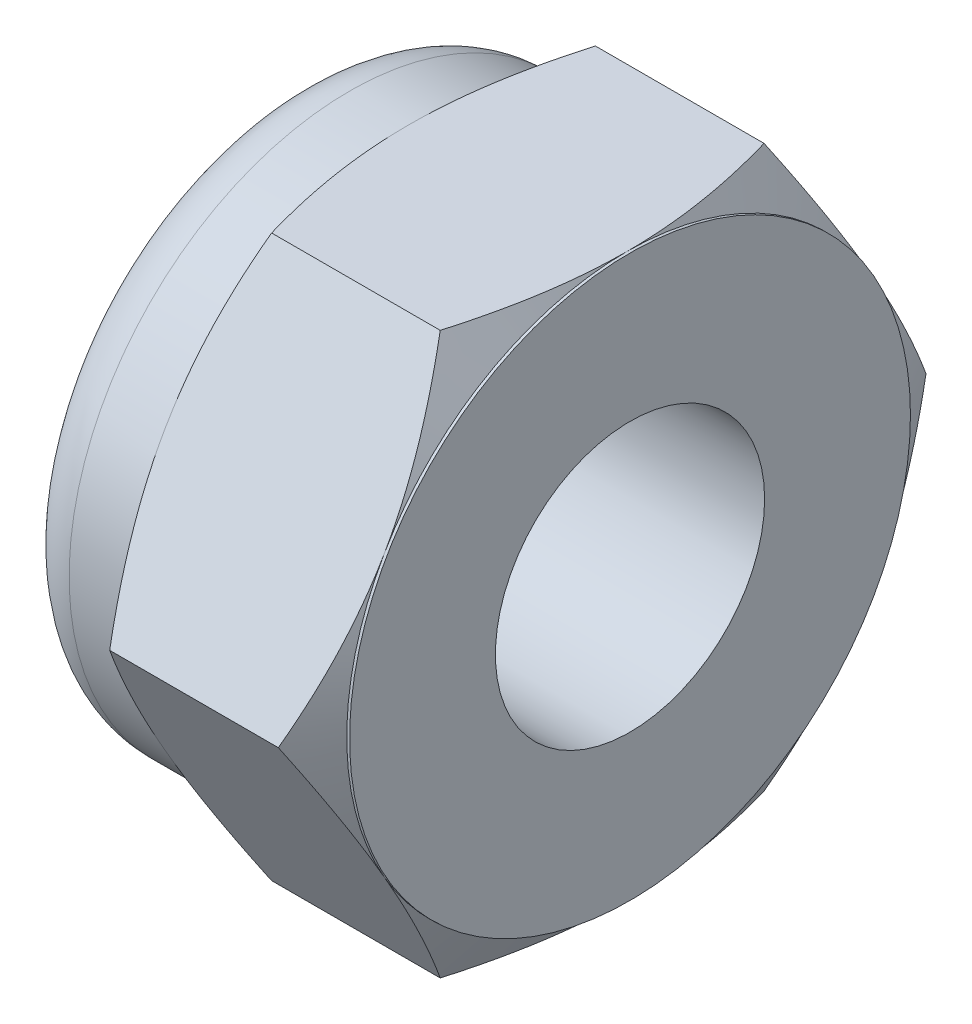
SolidWorks part; units mm, degrees
material " "
ref_plane "Ebene vorne" through (0, 0, 0) normal (0, 0, 1) x (1, 0, 0)
ref_plane "Ebene oben" through (0, 0, 0) normal (0, 1, 0) x (1, 0, 0)
ref_plane "Ebene rechts" through (0, 0, 0) normal (1, 0, 0) x (0, 0, -1)
sketch "Skizze6" plane through (0, 0, 0) normal (1, 0, 0) x (0, 0, -1)
  circle A0 centre (0, 0) radius 5
extrude "Grundkörper" add sketch "Skizze6" against normal blind 4 separate body
sketch "Skizze17" plane through (0, 0, 0) normal (0, 0, 1) x (1, 0, 0)
  line L0 (0, 0) -> (-4, 0) construction
  line L1 (3.3, 0) -> (-3.3, 0) construction
  line L2 (-4, 5) -> (-4, -5) construction
  line L3 (-0.05, 5) -> (-2, 8.3775)
  line L5 (-2, 8.3775) -> (-3.95, 5)
  line L6 (-3.95, 5) -> (-0.05, 5)
  line L7 (0, -5) -> (0, 5) construction
  line L8 (-2, 8.3775) -> (-2, 0) construction
  line L9 (0, 5) -> (-4, 5) construction
  dimension "D1" = 30
  dimension "D2" = 0.05
revolve "Rotation2" add sketch "Skizze17" angle 360 about L0
sketch "Skizze14" plane through (0, 0, 0) normal (1, 0, 0) x (0, 0, -1)
  line L1 (2.8868, -5) -> (5.7735, 0)
  line L2 (5.7735, 0) -> (2.8868, 5)
  line L3 (2.8868, 5) -> (-2.8868, 5)
  line L4 (-2.8868, 5) -> (-5.7735, 0)
  line L5 (-5.7735, 0) -> (-2.8868, -5)
  line L6 (-2.8868, -5) -> (2.8868, -5)
  circle A0 centre (0, 0) radius 5 construction
  circle A3 centre (0, 0) radius 8.3775 construction
  circle A4 centre (0, 0) radius 8.3775
extrude "Schnitt Sechskant" cut sketch "Skizze14" against normal through all
sketch "Skizze13" plane through (0, 0, 0) normal (1, 0, 0) x (0, 0, -1)
  circle A0 centre (0, 0) radius 2.4
extrude "Gewinde" cut sketch "Skizze13" against normal through all
cosmetic thread "Gewindedarstellung1"
sketch "Skizze18" plane through (0, 0, 0) normal (0, 0, 1) x (1, 0, 0)
  line L0 (0, 0) -> (-4, 0) construction
  line L1 (-4, 5) -> (-4, -5) construction
  line L2 (-4, 5) -> (-5, 5)
  line L3 (-6, 3) -> (-5, 3)
  line L4 (-6, 3) -> (-6, 4)
  line L5 (-4, 5) -> (-4, 4)
  line L8 (-4, 4) -> (-5, 4)
  line L9 (-5, 4) -> (-5, 3)
  arc A0 (-5, 5) -> (-6, 4) centre (-5, 4) ccw
  dimension "D1" = 1
  dimension "Sicherungsmutter_Höhe" = 6
revolve "Sicherungsmutter Rotation3" add sketch "Skizze18" angle 360 about L0
sketch "Skizze19" plane through (0, 0, 0) normal (0, 0, 1) x (1, 0, 0)
  line L0 (0, 0) -> (-3.0627, 0) construction
  line L1 (-5, 2.4) -> (-4, 2.4)
  line L2 (-5, 2.4) -> (-5, 4)
  line L3 (-5, 4) -> (-4, 4)
  line L4 (-4, 2.4) -> (-4, 4)
  line L6 (-5, -4) -> (-5, 4) construction
revolve "Sicherungsmutter Rotation4" add sketch "Skizze19" angle 360 about L0
sketch "Skizze20" [suppressed] plane through (0, 0, 0) normal (0, 0, 1) x (1, 0, 0)
  line L0 (0, 0) -> (-13, 0) construction
  line L1 (-13, 12) -> (-13, -12) construction
  line L2 (-13, 2.4) -> (-19, 2.4)
  line L3 (-19, 2.4) -> (-19, 12)
  line L4 (-19, 12) -> (-13, 12)
  line L5 (-13, 12) -> (-13, 2.4)
  line L6 (0, 2.4) -> (-13, 2.4) construction
  dimension "Kronenmutter_Höhe" = 8
revolve "Kronenmutter Rotation3" [suppressed] add sketch "Skizze20" angle 360 about L0
sketch "Skizze22" [suppressed] plane through (0, 0, 0) normal (0, 1, 0) x (1, 0, 0)
  line L0 (-19, 0) -> (-7, 0) construction
  line L1 (-19, 12) -> (-19, -12) construction
  line L2 (-3.3, 0) -> (3.3, 0) construction
  line L3 (-19, 1) -> (-7, 1)
  line L4 (-19, -1) -> (-7, -1)
  arc A0 (-19, 1) -> (-19, -1) centre (-19, 0) ccw
  arc A1 (-7, -1) -> (-7, 1) centre (-7, 0) ccw
  point P7 (-13, 0)
  dimension "Kopfhöhe" = 6
  dimension "D2" = 2
extrude "Kronenmutter Schnitt-Linear austragen1" [suppressed] cut sketch "Skizze22" against normal through all
pattern_circular "Kronenmutter Kreismuster1" [suppressed] count 6 over 360
sketch "Skizze23" [suppressed] plane through (0, 0, 0) normal (0, 0, 1) x (1, 0, 0)
  line L0 (-2.4, 2.75) -> (-3.25, 2.75)
  line L1 (-6, 0) -> (-3.8, 0)
  line L2 (-3.8, 0) -> (-3.1619, 1.2)
  line L3 (-3.1619, 1.2) -> (-2.4, 1.2)
  line L4 (-2.4, 1.2) -> (-2.4, 2.75)
  line L5 (-3.8, 0) -> (0, 0) construction
  arc A0 (-3.25, 2.75) -> (-6, 0) centre (-3.25, 0) ccw
  dimension "D1" = 118
  dimension "D2" = 2.2
  dimension "Hutmutterhöhe" = 12
  dimension "Hutmutter_Gewindetiefe" = 11.029
revolve "Hutmutter" [suppressed] add sketch "Skizze23" angle 360 about L5
sketch "Skizze24" [suppressed] plane through (0, 0, 0) normal (0, 1, 0) x (1, 0, 0)
  line L0 (0, 0) -> (-5, 0) construction
  line L1 (-5, 5.5) -> (-5, -5.5) construction
  line L2 (-0.35, 5.665) -> (-0.75, 5.4341)
  line L3 (0, -5.5) -> (0, 5.5) construction
  line L4 (-0.75, 5.4341) -> (-0.75, 4)
  line L5 (-0.75, 4) -> (0, 4)
  line L6 (0, 4) -> (0, 6.3509)
  line L7 (-0.35, 5.665) -> (-0.35, 6.3509)
  line L8 (-0.35, 6.3509) -> (0, 6.3509)
  line L9 (-4.4588, 6.3509) -> (-0.5412, 6.3509) construction
revolve "Schweißmutter" [suppressed] cut sketch "Skizze24" angle 360 about L0
equation "\"Innen@Skizze13\"=\"Gewinde\"*0.8"
equation "\"D1@Skizze6\" = \"Schlüsselweite@Skizze14\""
equation "\"D3@Skizze24\"=\"Schlüsselweite@Skizze14\" * 1.03"
